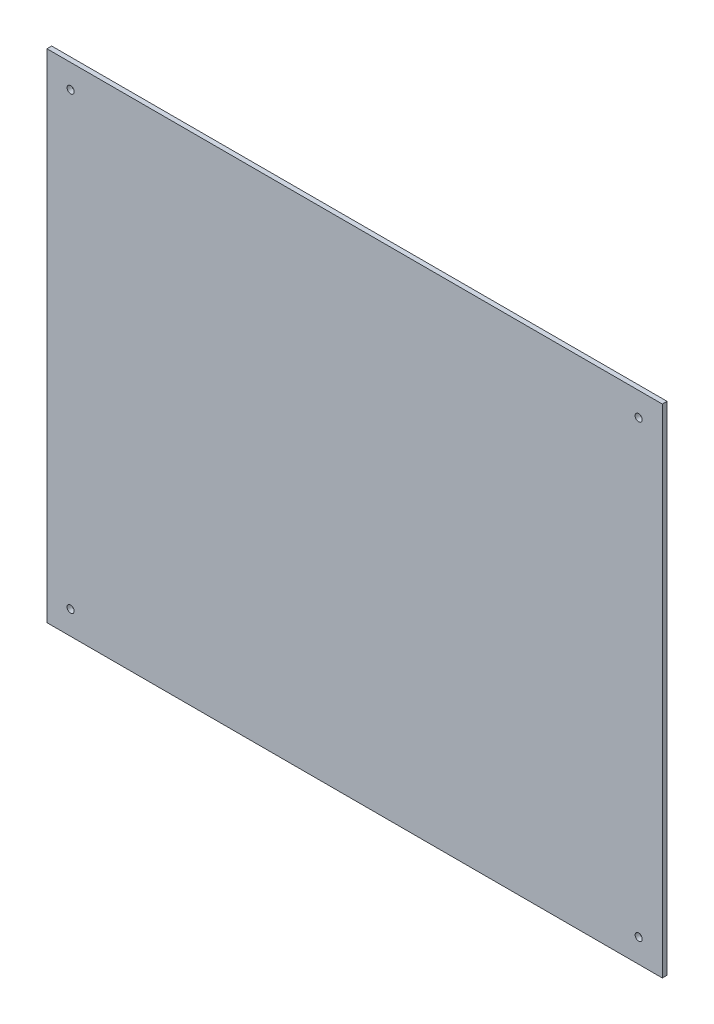
SolidWorks part; units mm, degrees
ref_plane "前视基准面" through (0, 0, 0) normal (0, 0, 1) x (1, 0, 0)
ref_plane "上视基准面" through (0, 0, 0) normal (0, 1, 0) x (1, 0, 0)
ref_plane "右视基准面" through (0, 0, 0) normal (1, 0, 0) x (0, 0, -1)
sketch "草图1" plane through (0, 0, 0) normal (0, 0, 1) x (1, 0, 0)
  line L0 (0, 0) -> (260, 0)
  line L1 (260, 0) -> (260, 210)
  line L2 (260, 210) -> (0, 210)
  line L3 (0, 210) -> (0, 0)
  dimension "D1" = 260
  dimension "D2" = 210
extrude "凸台-拉伸1" add sketch "草图1" along normal blind 2
sketch "草图2" plane through (0, 0, 2) normal (0, 0, 1) x (1, 0, 0)
  circle A0 centre (10, 200) radius 1.5
  circle A1 centre (250, 200) radius 1.5
  circle A2 centre (10, 10) radius 1.5
  circle A3 centre (250, 10) radius 1.5
extrude "切除-拉伸1" cut sketch "草图2" against normal blind 2
